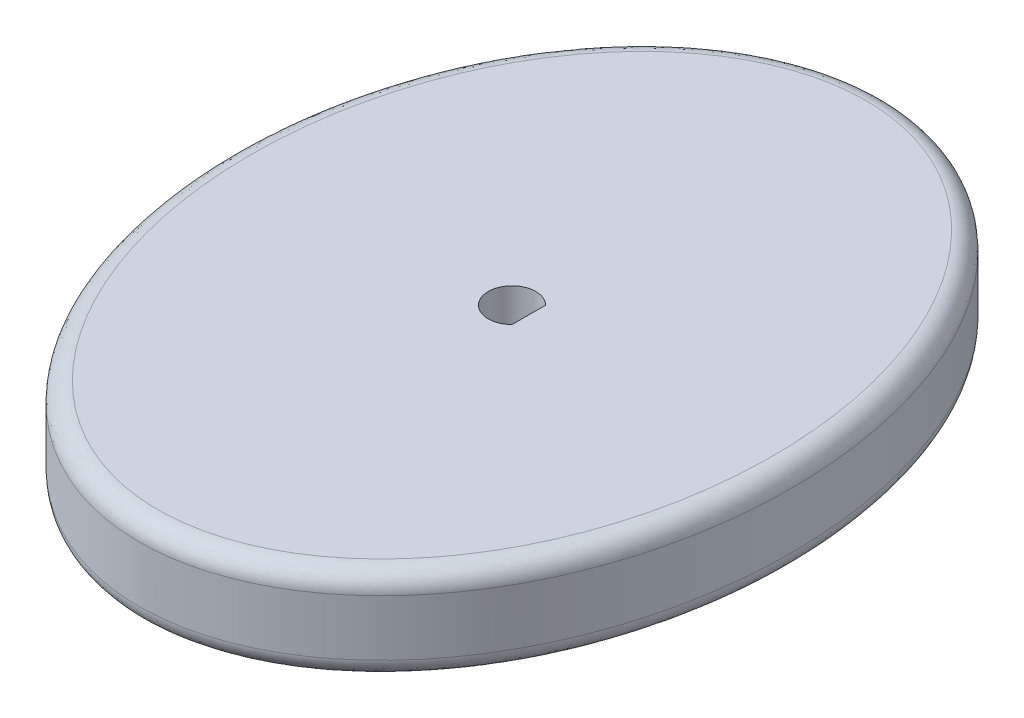
SolidWorks part; units mm, degrees
ref_plane "Front Plane" through (0, 0, 0) normal (0, 0, 1) x (1, 0, 0)
ref_plane "Top Plane" through (0, 0, 0) normal (0, 1, 0) x (1, 0, 0)
ref_plane "Right Plane" through (0, 0, 0) normal (1, 0, 0) x (0, 0, -1)
sketch "Sketch2" plane through (0, 0, 0) normal (0, 1, 0) x (1, 0, 0)
  line L0 (1.143, -1.147) -> (1.143, 1.147)
  arc A2 (1.143, 1.147) -> (1.143, -1.147) centre (0, 0) ccw
  ellipse E0 centre (0, 0) end of major axis (0, 25.4) minor radius 19.05
  dimension "D3" = 3.2385
  dimension "D1" = 25.4
  dimension "D2" = 19.05
  dimension "D4" = 1.143
extrude "Crank" add sketch "Sketch2" along normal blind 6.35
fillet "Fillet" radius 1.27 2 edges at (0, 0, -25.4) (0, 6.35, -25.4)
equation "\"Motor Shaft Diam\"= .1175in"
equation "\"Stroke Length\"= .5"
equation "\"D3@Sketch2\"=\"Motor Shaft Diam\"+.01"
equation "\"Binding Post Diam\"= 5 / 16"
